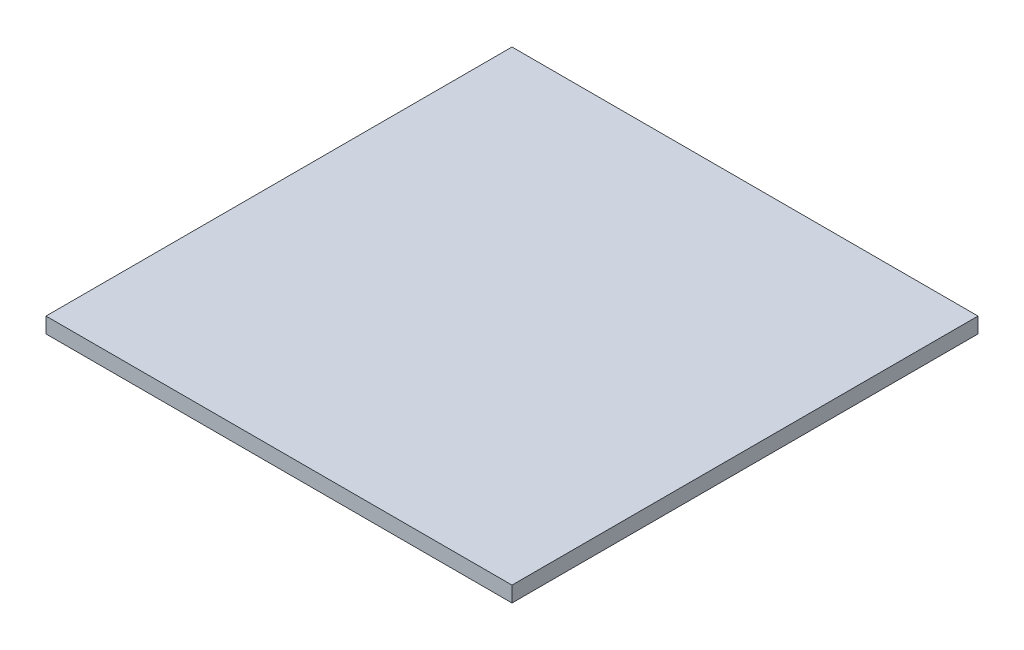
SolidWorks part; units mm, degrees
ref_plane "Front Plane" through (0, 0, 0) normal (0, 0, 1) x (1, 0, 0)
ref_plane "Top Plane" through (0, 0, 0) normal (0, 1, 0) x (1, 0, 0)
ref_plane "Right Plane" through (0, 0, 0) normal (1, 0, 0) x (0, 0, -1)
sketch "Sketch1" plane through (0, 0, 0) normal (0, 1, 0) x (1, 0, 0)
  line L1 (0, 0) -> (300, 0)
  line L2 (0, 0) -> (0, 300)
  line L3 (0, 300) -> (300, 300)
  line L4 (300, 0) -> (300, 300)
  dimension "D1" = 300
  dimension "D2" = 300
extrude "Boss-Extrude1" add sketch "Sketch1" along normal blind 10
